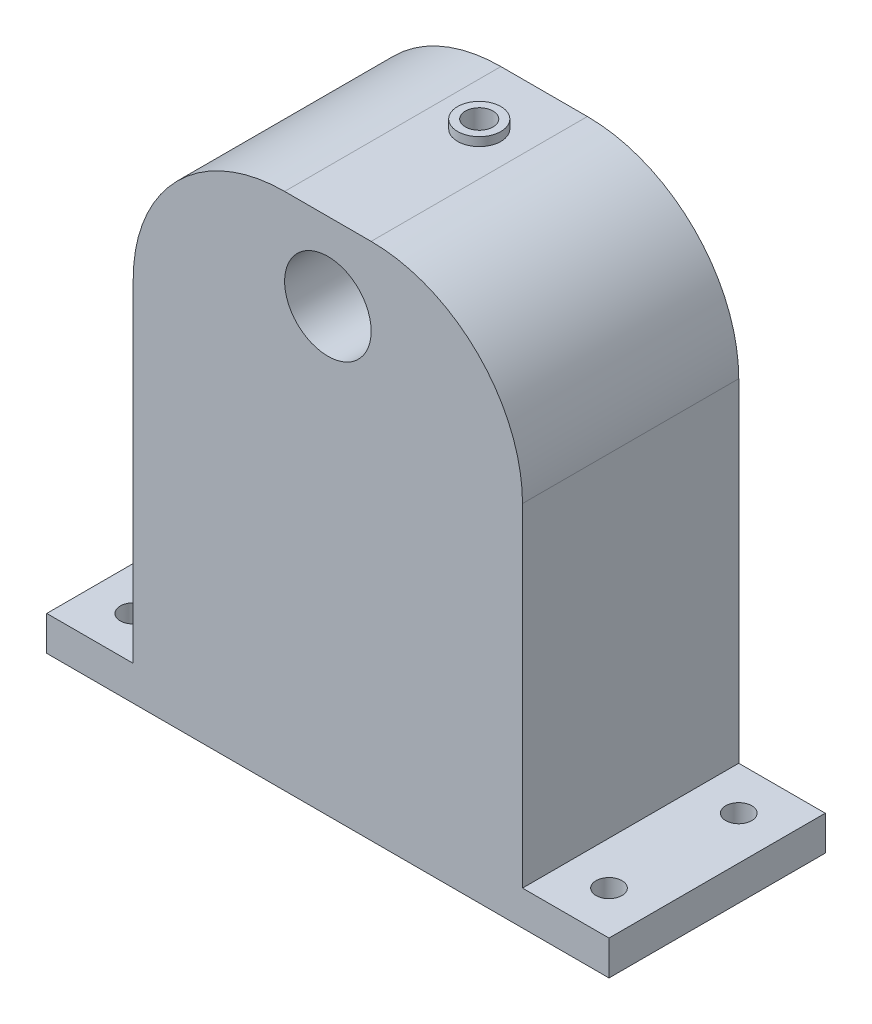
SolidWorks part; units mm, degrees
material "ABS"
ref_plane "Front Plane" through (0, 0, 0) normal (0, 0, 1) x (1, 0, 0)
ref_plane "Top Plane" through (0, 0, 0) normal (0, 1, 0) x (1, 0, 0)
ref_plane "Right Plane" through (0, 0, 0) normal (1, 0, 0) x (0, 0, -1)
sketch "Sketch1" plane through (0, 0, 0) normal (0, 1, 0) x (1, 0, 0)
  line L2 (-32.5, -7.5) -> (-32.5, 7.5)
  line L3 (-32.5, 7.5) -> (32.5, 7.5)
  line L4 (32.5, 7.5) -> (32.5, -7.5)
  line L5 (32.5, -7.5) -> (-32.5, -7.5)
extrude "Boss-Extrude1" add sketch "Sketch1" along normal blind 4
sketch "Sketch2" plane through (0, 4, 0) normal (0, 1, 0) x (1, 0, 0)
  line L1 (-32.5, -7.5) -> (32.5, -7.5) construction
  line L3 (-22.5, -7.5) -> (-22.5, 7.5)
  line L4 (32.5, 7.5) -> (-32.5, 7.5) construction
  line L5 (-22.5, 7.5) -> (22.5, 7.5)
  line L6 (22.5, 7.5) -> (22.5, -7.5)
  line L7 (22.5, -7.5) -> (-22.5, -7.5)
extrude "Boss-Extrude2" add sketch "Sketch2" along normal blind 56
sketch "Sketch3" plane through (0, 0, 7.5) normal (0, 0, 1) x (1, 0, 0)
  circle A0 centre (0, 51) radius 5
extrude "Cut-Extrude1" cut sketch "Sketch3" against normal blind 10
sketch "Sketch6" plane through (0, 0, 7.5) normal (0, 0, 1) x (1, 0, 0)
  line L1 (-22.5, 60) -> (22.5, 60) construction
  line L9 (22.5, 60) -> (22.5, 4) construction
  line L11 (5, 60) -> (22.5, 60)
  line L13 (22.5, 60) -> (22.5, 42.5)
  line L14 (-22.5, 42.5) -> (-22.5, 60)
  line L15 (-22.5, 60) -> (-5, 60)
  arc A4 (-5, 60) -> (-22.5, 42.5) centre (-5, 42.5) ccw
  arc A5 (22.5, 42.5) -> (5, 60) centre (5, 42.5) ccw
extrude "Cut-Extrude5" cut sketch "Sketch6" against normal up to next
sketch "Sketch7" plane through (0, 0, -7.5) normal (0, 0, -1) x (-1, 0, 0)
  line L0 (-22.5, 42.5) -> (-22.5, 4) construction
  line L1 (-32.5, 4) -> (-22.5, 4) construction
  line L2 (-32.5, 4) -> (-32.5, 0) construction
  line L3 (-32.5, 0) -> (32.5, 0) construction
  line L4 (32.5, 4) -> (32.5, 0) construction
  line L5 (22.5, 4) -> (32.5, 4) construction
  line L6 (22.5, 42.5) -> (22.5, 4) construction
  line L7 (-5, 60) -> (5, 60) construction
  line L8 (-22.5, 42.5) -> (-22.5, 4)
  line L9 (-32.5, 4) -> (-22.5, 4)
  line L10 (-32.5, 4) -> (-32.5, 0)
  line L11 (-32.5, 0) -> (32.5, 0)
  line L12 (32.5, 4) -> (32.5, 0)
  line L13 (22.5, 4) -> (32.5, 4)
  line L14 (22.5, 42.5) -> (22.5, 4)
  line L15 (-5, 60) -> (5, 60)
  arc A0 (-5, 60) -> (-22.5, 42.5) centre (-5, 42.5) ccw construction
  arc A1 (22.5, 42.5) -> (5, 60) centre (5, 42.5) ccw construction
  arc A2 (-5, 60) -> (-22.5, 42.5) centre (-5, 42.5) ccw
  arc A3 (22.5, 42.5) -> (5, 60) centre (5, 42.5) ccw
extrude "Boss-Extrude3" add sketch "Sketch7" along normal blind 10
sketch "Sketch8" plane through (0, 4, 0) normal (0, 1, 0) x (1, 0, 0)
  circle A0 centre (-27.5, -2.5) radius 1.5
  circle A1 centre (-27.5, 12.5) radius 1.5
  circle A2 centre (27.5, 12.5) radius 1.5
  circle A3 centre (27.5, -2.5) radius 1.5
extrude "Cut-Extrude6" cut sketch "Sketch8" against normal up to next
sketch "Sketch9" plane through (0, 60, 0) normal (0, 1, 0) x (1, 0, 0)
  line L0 (-2.875, 11.6599) -> (-2.875, 17.5)
  line L2 (-5, 17.5) -> (5, 17.5) construction
  line L3 (-2.875, 17.5) -> (2.875, 17.5)
  line L4 (-2.875, 11.6599) -> (-2.875, 8.3401)
  line L5 (-2.875, 8.3401) -> (0, 6.6802)
  line L6 (0, 6.6802) -> (2.875, 8.3401)
  line L7 (2.875, 8.3401) -> (2.875, 11.6599)
  line L8 (2.875, 17.5) -> (2.875, 11.6599)
  line L9 (0, 13.3198) -> (-2.875, 11.6599) [skipped]
  line L10 (2.875, 11.6599) -> (0, 13.3198) [skipped]
extrude "Cut-Extrude7" cut sketch "Sketch9" against normal blind 22.5
sketch "Sketch10" plane through (0, 60, 0) normal (0, 1, 0) x (1, 0, 0)
  line L0 (0, 6.6802) -> (2.875, 8.3401) construction
  line L3 (2.875, 8.3401) -> (2.875, 17.5) construction
  line L4 (0, 6.6802) -> (2.875, 8.3401)
  line L5 (-2.875, 8.3401) -> (-2.875, 17.5)
  line L7 (2.875, 8.3401) -> (2.875, 17.5)
  line L8 (2.875, 17.5) -> (-2.875, 17.5)
  line L9 (0, 6.6802) -> (-2.875, 8.3401)
  circle A1 centre (0, 10) radius 1.6
extrude "Boss-Extrude4" add sketch "Sketch10" against normal blind 20
sketch "Sketch11" plane through (0, 60, 0) normal (0, 1, 0) x (1, 0, 0)
  circle A0 centre (0, 10) radius 1.6 construction
  circle A1 centre (0, 10) radius 1.6
extrude "Cut-Extrude8" cut sketch "Sketch11" against normal blind 35
sketch "Sketch12" plane through (0, 60, 0) normal (0, 1, 0) x (1, 0, 0)
  circle A0 centre (0, 10) radius 2.5
  circle A1 centre (0, 10) radius 1.6 construction
  circle A2 centre (0, 10) radius 1.6
extrude "Boss-Extrude5" add sketch "Sketch12" along normal blind 1
